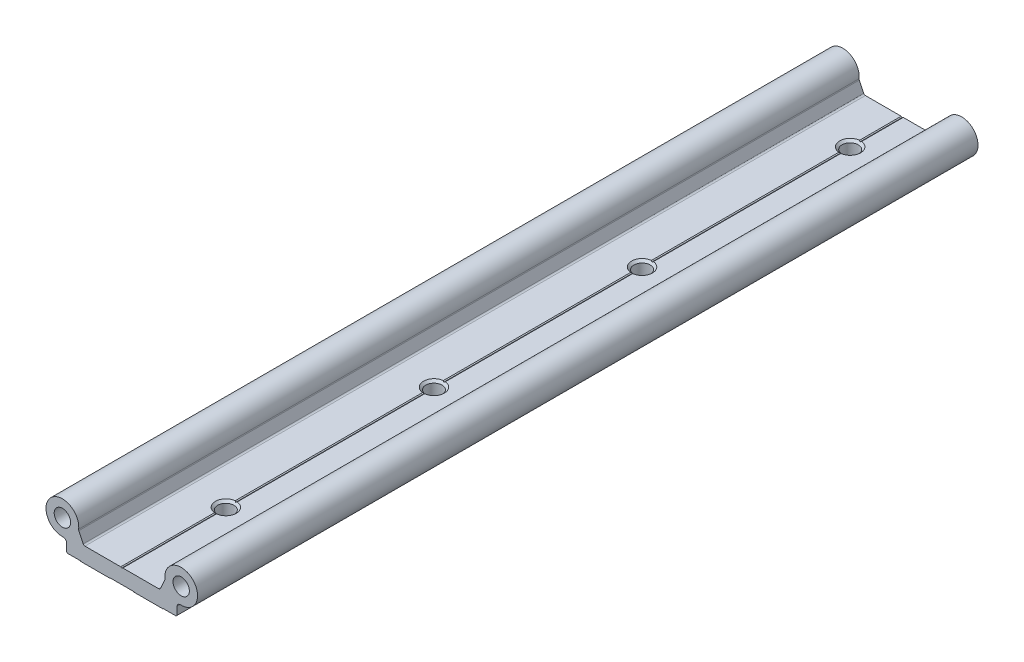
SolidWorks part; units mm, degrees
ref_plane "Front Plane" through (0, 0, 0) normal (0, 0, 1) x (1, 0, 0)
ref_plane "Top Plane" through (0, 0, 0) normal (0, 1, 0) x (1, 0, 0)
ref_plane "Right Plane" through (0, 0, 0) normal (1, 0, 0) x (0, 0, -1)
sketch "Model" plane through (0, 0, 0) normal (0, 0, 1) x (1, 0, 0)
  line L0 (0, 0.2) -> (0, 7.5) construction
  line L1 (0, 0.2) -> (0, 7.5) construction
  line L2 (0, 0.2) -> (0, 7.5) construction
  line L3 (0, 0.2) -> (0, 7.5) construction
  line L4 (-33, 14) -> (-25, 14) construction
  line L5 (25, 14) -> (33, 14) construction
  line L6 (-29, 22) -> (-29, 6) construction
  line L7 (-37, 14) -> (-21, 14) construction
  line L8 (29, 22) -> (29, 6) construction
  line L9 (21, 14) -> (37, 14) construction
  line L10 (-18.8438, 7.9819) -> (-20.9669, 12.5349)
  line L11 (6, 0) -> (5.8, 0.2)
  line L12 (-26.5, 0.2) -> (-27, 0.7)
  line L13 (-20, 0) -> (-20.2, 0.2)
  line L14 (0, 7.2113) -> (-0.5, 7.5)
  line L15 (6, 0) -> (20, 0)
  line L16 (-20, 0) -> (-6, 0)
  line L17 (-5.8, 0.2) -> (5.8, 0.2)
  line L18 (20.2, 0.2) -> (26.5, 0.2)
  line L19 (-26.5, 0.2) -> (-20.2, 0.2)
  line L20 (0.5, 7.5) -> (17.9885, 7.5)
  line L21 (-17.9885, 7.5) -> (-0.5, 7.5)
  line L22 (0, 7.2113) -> (0.5, 7.5)
  line L23 (20, 0) -> (20.2, 0.2)
  line L24 (-6, 0) -> (-5.8, 0.2)
  line L25 (26.5, 0.2) -> (27, 0.7)
  line L26 (18.8438, 7.9819) -> (20.9669, 12.5349)
  line L27 (-27, 0.7) -> (-27, 4.5132)
  line L28 (27, 0.7) -> (27, 4.5132)
  circle A0 centre (-29, 14) radius 4
  arc A1 (-21.0538, 13.0733) -> (-28.5789, 6.0111) centre (-29, 14) ccw
  arc A2 (-27, 4.5132) -> (-28.5789, 6.0111) centre (-28.5, 4.5132) ccw
  arc A3 (-21.0538, 13.0733) -> (-20.9669, 12.5349) centre (-20.0606, 12.9575) ccw
  arc A4 (-18.8438, 7.9819) -> (-17.9885, 7.5) centre (-17.9885, 8.5) ccw
  arc A5 (17.9885, 7.5) -> (18.8438, 7.9819) centre (17.9885, 8.5) ccw
  arc A6 (20.9669, 12.5349) -> (21.0538, 13.0733) centre (20.0606, 12.9575) ccw
  arc A7 (28.5789, 6.0111) -> (27, 4.5132) centre (28.5, 4.5132) ccw
  circle A8 centre (29, 14) radius 4
  arc A9 (28.5789, 6.0111) -> (21.0538, 13.0733) centre (29, 14) ccw
  dimension "D1" = 8
  dimension "D2" = 8
  dimension "D3" = 1.5
  dimension "D4" = 1
  dimension "D5" = 0.5
  dimension "D6" = 5.8
  dimension "D7" = 6
  dimension "D8" = 17.9885
  dimension "D9" = 18.8438
  dimension "D10" = 20
  dimension "D11" = 20.0606
  dimension "D12" = 20.9669
  dimension "D13" = 21.0538
  dimension "D14" = 26.5
  dimension "D15" = 27
  dimension "D16" = 4.5132
  dimension "D17" = 7.2113
extrude "Boss-Extrude1" add sketch "Model" along normal blind 381
hole_wizard "3/8-16 Tapped Hole1" positions "Sketch1" profile "Sketch2" tap size "3/8-16" standard "ANSI Inch" end condition through all
sketch "Sketch1" plane through (0, 7.5, 0) normal (0, 1, 0) x (1, 0, 0)
  line L0 (0, -381) -> (0, 0) construction
  line L1 (-0.5, 0) -> (-17.9885, 0) construction
  point P0 (0, -25.4)
  point P21 (0, -127)
  point P22 (0, -228.6)
  point P23 (0, -330.2)
  point P24 (0, -431.8)
  point P25 (0, -533.4)
  point P26 (0, -635)
  point P27 (0, -736.6)
  point P28 (0, -838.2)
  point P29 (0, -939.8)
  point P30 (0, -1041.4)
  point P31 (0, -1143)
  point P32 (0, -1244.6)
  point P33 (0, -1346.2)
  point P34 (0, -1447.8)
  point P35 (0, -1549.4)
  point P36 (0, -1651)
  point P37 (0, -1752.6)
  point P38 (0, -1854.2)
  point P39 (0, -1955.8)
  dimension "D1" = 25.4
  dimension "D2" = 20
sketch "Sketch2" plane through (0, 7.5, 25.4) normal (1, 0, 0) x (0, 0, 1)
  line L0 (0, 0) -> (0, 7.5)
  line L1 (0, 7.5) -> (3.9687, 7.5)
  line L2 (3.9687, 7.5) -> (3.9687, 1.1113)
  line L3 (3.9687, 1.1113) -> (5.08, 0)
  line L5 (5.08, 0) -> (0, 0)
  line L6 (-3.9687, 1.1112) -> (-5.08, 0) construction
  line L11 (0, -6.35) -> (0, 107.95) construction
  dimension "Thread Major Dia." = 7.9375
  dimension "Thru Tap Drill Depth" = 7.5
  dimension "Near C'Sink Dia." = 10.16
  dimension "Near C'Sink Angle" = 90
